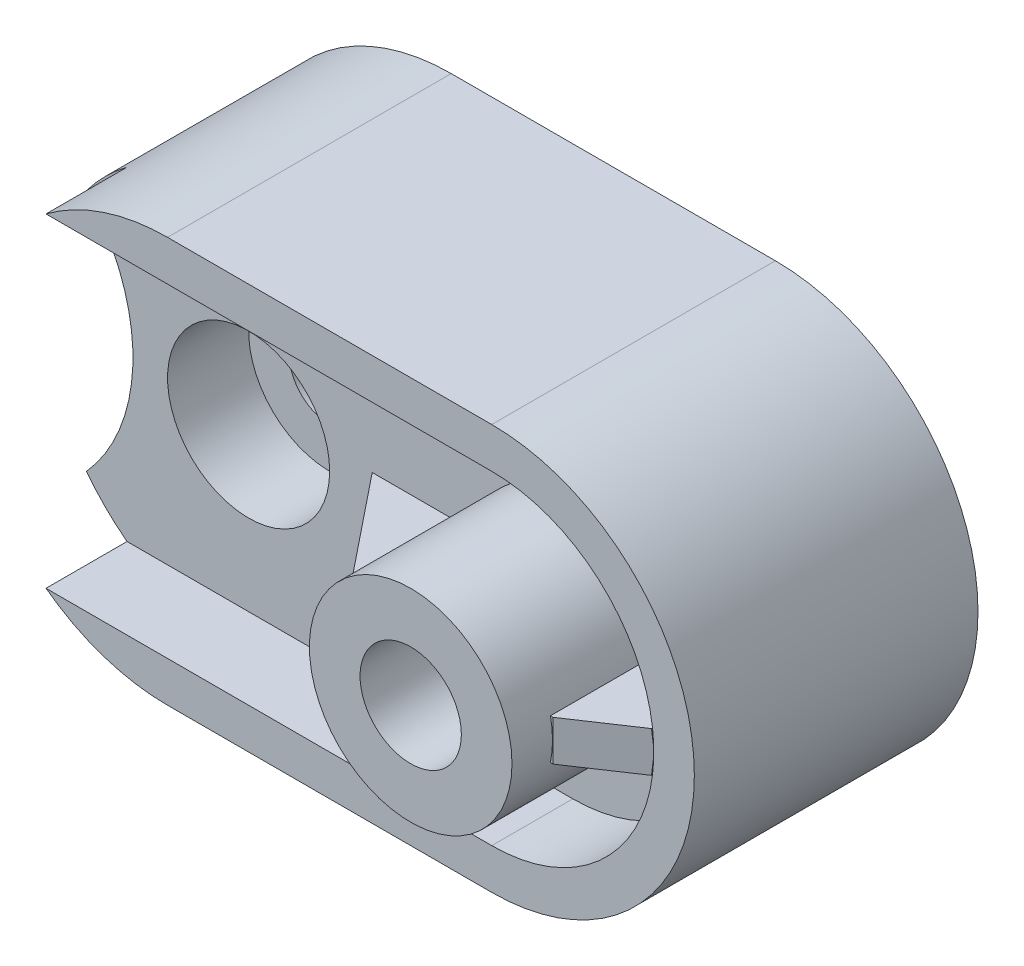
SolidWorks part; units mm, degrees
ref_plane "Front Plane" through (0, 0, 0) normal (0, 0, 1) x (1, 0, 0)
ref_plane "Top Plane" through (0, 0, 0) normal (0, 1, 0) x (1, 0, 0)
ref_plane "Right Plane" through (0, 0, 0) normal (1, 0, 0) x (0, 0, -1)
sketch "Sketch1" plane through (0, 0, 0) normal (0, 0, 1) x (1, 0, 0)
  line L1 (0, 0) -> (180, 0)
  line L2 (0, 0) -> (0, 100)
  line L3 (0, 100) -> (180, 100)
  line L4 (180, 0) -> (180, 100)
  dimension "D1" = 100
  dimension "D2" = 180
extrude "Boss-Extrude2" add sketch "Sketch1" along normal blind 70
sketch "Sketch2" plane through (0, 0, 70) normal (0, 0, 1) x (1, 0, 0)
  line L0 (180, 100) -> (0, 100) construction
  line L2 (180, 0) -> (180, 100) construction
  line L4 (0, 100) -> (180, 100)
  line L5 (0, 100) -> (0, 0)
  line L6 (0, 0) -> (180, 0)
  line L7 (180, 100) -> (180, 0)
  arc A0 (50, 100) -> (50, 0) centre (50, 50) ccw
  arc A1 (130, 100) -> (130, 0) centre (130, 50) cw
  line M1 (0, 100) -> (0, 0)
  line M2 (0, 0) -> (180, 0)
  line M3 (180, 0) -> (180, 100)
  line M4 (180, 100) -> (0, 100)
  dimension "D9" = 50
  dimension "D1" = 50
  dimension "D2" = 50
  dimension "D3" = 50
  dimension "D4" = 50
  dimension "D5" = 50
  dimension "D6" = 50
  dimension "D7" = 50
  dimension "D8" = 50
extrude "Cut-Extrude1" cut sketch "Sketch2" against normal blind 70 contours A0 L4 M1 | A0 L5 M2 | A1 M3 M2 | A1 L7 M4
sketch "Sketch3" plane through (0, 0, 70) normal (0, 0, 1) x (1, 0, 0)
  circle A0 centre (10, 50) radius 5
  arc A1 (50, 100) -> (50, 0) centre (50, 50) ccw construction
  point P2 (0, 50)
  dimension "D1" = 10
  dimension "D2" = 50
  dimension "D3" = 10
extrude "Cut-Extrude2" cut sketch "Sketch3" against normal blind 70
sketch "Sketch4" plane through (0, 0, 70) normal (0, 0, 1) x (1, 0, 0)
  arc A0 (10, 80) -> (10, 20) centre (-23.541, 50) cw
  arc A1 (50, 100) -> (50, 0) centre (50, 50) ccw construction
  arc A2 (10, 80) -> (10, 20) centre (50, 50) ccw
  circle M1 centre (10, 50) radius 5
  arc M4 (50, 100) -> (50, 0) centre (50, 50) ccw
  dimension "D1" = 40
  dimension "D5" = 45
  dimension "D2" = 40
  dimension "D3" = 20
  dimension "D4" = 20
extrude "Cut-Extrude3" cut sketch "Sketch4" against normal blind 50 contours A0 M4 M1
sketch "Sketch5" plane through (0, 0, 70) normal (0, 0, 1) x (1, 0, 0)
  circle A0 centre (50, 50) radius 10
  dimension "D1" = 20
extrude "Cut-Extrude4" cut sketch "Sketch5" against normal blind 106
sketch "Sketch6" plane through (0, 0, 70) normal (0, 0, 1) x (1, 0, 0)
  circle A0 centre (130, 50) radius 15
  dimension "D1" = 30
extrude "Cut-Extrude5" cut sketch "Sketch6" against normal blind 40
sketch "Sketch7" plane through (0, 0, 70) normal (0, 0, 1) x (1, 0, 0)
  point P0 (130, 50)
sketch "Sketch8" plane through (0, 0, 70) normal (0, 0, 1) x (1, 0, 0)
  circle A0 centre (130, 50) radius 15
  circle A1 centre (130, 50) radius 12.5
  dimension "D1" = 30
  dimension "D2" = 25
extrude "Boss-Extrude3" add sketch "Sketch8" against normal blind 40
sketch "Sketch10" plane through (0, 0, 70) normal (0, 0, 1) x (1, 0, 0)
  circle A0 centre (130, 50) radius 12.5
  dimension "D1" = 25
extrude "Boss-Extrude4" add sketch "Sketch10" against normal blind 65
hole_wizard "Ø25.0mm Dowel Hole2" positions "3DSketch2" profile "Sketch11" hole size "Ø25.0" standard "ISO"
sketch3d "3DSketch2"
  point P0 (130, 50, 70)
sketch "Sketch11" plane through (130, 50, 70) normal (1, 0, 0) x (0, -1, 0)
  line L0 (0, 0) -> (0, 27.5108)
  line L1 (0, 27.5108) -> (12.5, 20)
  line L2 (12.5, 20) -> (12.5, 0)
  line L5 (12.5, 0) -> (0, 0)
  line L10 (0, 27.5108) -> (-12.5, 20) construction
  line L11 (0, -6.35) -> (0, 107.95) construction
  dimension "Hole Dia." = 25
  dimension "Hole Depth" = 20
  dimension "Drill Angle" = 118
sketch "Sketch12" plane through (0, 0, 70) normal (0, 0, 1) x (1, 0, 0)
  line L0 (130, 90) -> (20, 90)
  line L2 (130, 10) -> (20, 10)
  line L3 (130, 100) -> (50, 100) construction
  line L4 (50, 100) -> (130, 100)
  line L5 (50, 0) -> (130, 0) construction
  line L6 (130, 0) -> (50, 0)
  arc A0 (130, 90) -> (130, 10) centre (130, 50) cw
  arc A3 (10, 80) -> (10, 20) centre (50, 50) ccw construction
  arc A4 (10, 20) -> (50, 0) centre (50, 50) ccw construction
  arc A5 (20, 90) -> (50, 100) centre (50, 50) cw
  arc A6 (130, 100) -> (130, 0) centre (130, 50) cw
  arc A7 (20, 10) -> (50, 0) centre (50, 50) ccw
  point P4 (0, 50)
  circle M1 centre (130, 50) radius 12.5
  circle M2 centre (50, 50) radius 10
  arc M3 (10, 80) -> (10, 20) centre (-23.541, 50) cw
  arc M4 (10, 20) -> (50, 0) centre (50, 50) ccw
  arc M8 (50, 100) -> (10, 80) centre (50, 50) ccw
  dimension "D3" = 40
  dimension "D1" = 10
  dimension "D2" = 10
  dimension "D4" = 110
  dimension "D5" = 20
extrude "Cut-Extrude6" cut sketch "Sketch12" against normal blind 20 contours A0 L0 L2 M8 M3 M4 M2 M1
sketch "Sketch13" plane through (0, 0, 50) normal (0, 0, 1) x (1, 0, 0)
  circle A0 centre (130, 50) radius 12.5
  circle A1 centre (130, 50) radius 25
  dimension "D1" = 25
  dimension "D2" = 50
extrude "Boss-Extrude5" add sketch "Sketch13" along normal blind 40
sketch "Sketch14" plane through (0, 0, 50) normal (0, 0, 1) x (1, 0, 0)
  circle A0 centre (50, 50) radius 10
  circle A1 centre (50, 50) radius 20
  dimension "D1" = 20
  dimension "D2" = 40
extrude "Cut-Extrude7" cut sketch "Sketch14" against normal blind 20
sketch "Sketch15" plane through (0, 0, 50) normal (0, 0, 1) x (1, 0, 0)
  line L1 (105.5051, 55) -> (80.5051, 55)
  line L2 (105.5051, 55) -> (105.5051, 45)
  line L3 (105.5051, 45) -> (80.5051, 45)
  line L4 (80.5051, 55) -> (80.5051, 45)
  line L5 (154.4949, 55) -> (169.6863, 55)
  line L6 (154.4949, 55) -> (154.4949, 45)
  line L7 (154.4949, 45) -> (169.6863, 45)
  line L8 (169.6863, 55) -> (169.6863, 45)
  circle A0 centre (130, 50) radius 25 construction
  arc A1 (130, 10) -> (130, 90) centre (130, 50) ccw construction
  arc A3 (105.5051, 55) -> (105.5051, 45) centre (130, 50) ccw
  arc A4 (154.4949, 55) -> (154.4949, 45) centre (130, 50) cw
  circle M8 centre (130, 50) radius 25
  dimension "D1" = 10
  dimension "D2" = 10
  dimension "D3" = 45
  dimension "D4" = 45
  dimension "D5" = 25
extrude "Boss-Extrude10" add sketch "Sketch15" along normal blind 30 contours L2 M8 | L1 L4 L3 M8
sketch "Sketch16" plane through (0, 0, 50) normal (0, 0, 1) x (1, 0, 0)
  line L1 (154.4949, 55) -> (170, 55)
  line L2 (154.4949, 55) -> (154.4949, 45)
  line L3 (154.4949, 45) -> (170, 45)
  line L4 (170, 55) -> (170, 45)
  arc A0 (105.5051, 45) -> (105.5051, 55) centre (130, 50) ccw construction
  arc A1 (130, 10) -> (130, 90) centre (130, 50) ccw construction
  arc A2 (154.4949, 55) -> (154.4949, 45) centre (130, 50) cw
  arc A3 (170, 55) -> (170, 45) centre (130, 50) cw
  arc M1 (130, 10) -> (130, 90) centre (130, 50) ccw
  arc M10 (105.5051, 55) -> (105.5051, 45) centre (130, 50) cw
  dimension "D1" = 45
  dimension "D2" = 10
extrude "Boss-Extrude13" add sketch "Sketch16" along normal blind 30 contours L3 L1 M10 M1
ref_plane "Plane1" through (0, 50, 0) normal (0, 1, 0) x (1, 0, 0)
sketch "Sketch18" plane through (0, 50, 0) normal (0, 1, 0) x (1, 0, 0)
  line L0 (155.157, -80) -> (170.0986, -70)
  line L1 (154.4949, -80) -> (169.6863, -80) construction
  line L2 (154.4949, -80) -> (155, -80) construction
  line L3 (130, -70) -> (180, -70) construction
  line L4 (170.0986, -70) -> (170.0986, -80)
  line L5 (169.6863, -80) -> (170, -80) construction
  line L6 (170.0986, -80) -> (155.157, -80)
  line L7 (104.5789, -80) -> (80.5051, -50)
  line L8 (105.5051, -80) -> (80.5051, -80) construction
  line L9 (80.5051, -50) -> (80.5051, -80)
  line L10 (80.5051, -80) -> (104.5789, -80)
extrude "Cut-Extrude8" cut sketch "Sketch18" against normal mid plane 10
